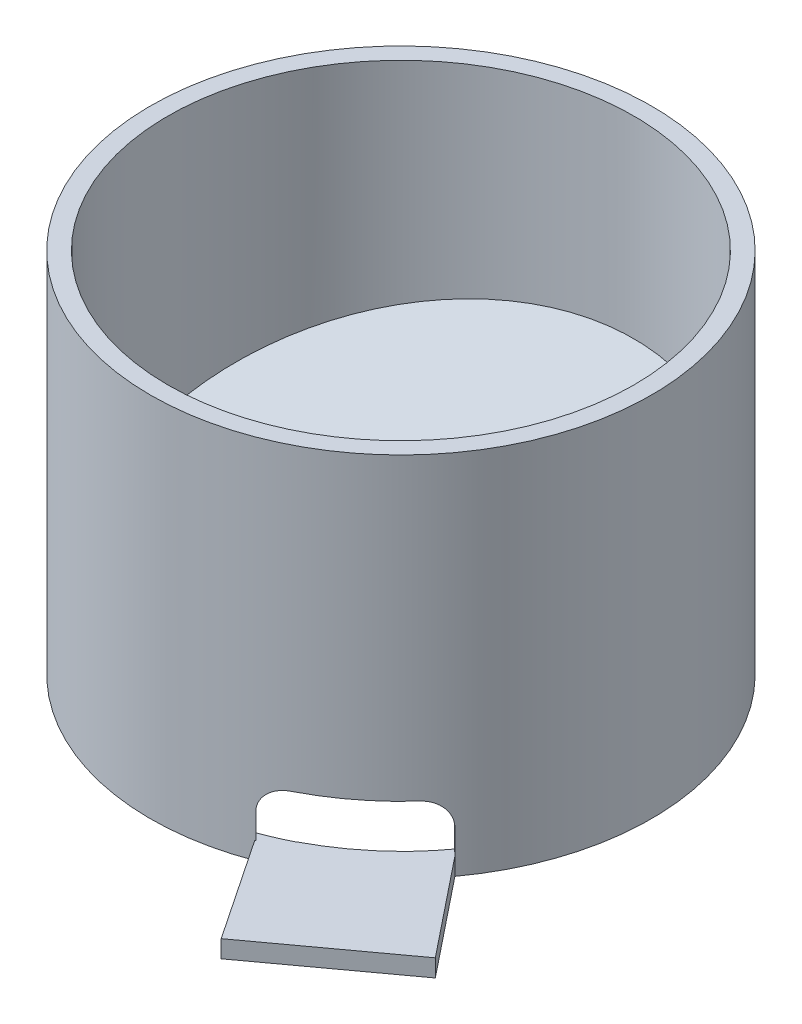
SolidWorks part; units mm, degrees
ref_plane "Front Plane" through (0, 0, 0) normal (0, 0, 1) x (1, 0, 0)
ref_plane "Top Plane" through (0, 0, 0) normal (0, 1, 0) x (1, 0, 0)
ref_plane "Right Plane" through (0, 0, 0) normal (1, 0, 0) x (0, 0, -1)
sketch "Sketch1" plane through (0, 0, 0) normal (0, 1, 0) x (1, 0, 0)
  line L0 (-85.6178, 0) -> (101.9259, 0) construction
  line L1 (0, 82.0843) -> (0, -78.0073) construction
  circle A0 centre (0, 0) radius 40
  circle A1 centre (0, 0) radius 43
extrude "Boss-Extrude1" add sketch "Sketch1" along normal blind 63
ref_plane "Plane1" through (0, 0, 0) normal (0, -1, 0) x (-1, 0, 0)
sketch "Sketch2" plane through (0, 0, 0) normal (0, -1, 0) x (-1, 0, 0)
  line L0 (-73.177, 0) -> (71.4567, 0) construction
  line L1 (0, 50.2844) -> (0, -53.4602) construction
  circle A0 centre (0, 0) radius 41.5
  circle A1 centre (0, 0) radius 40
extrude "Cut-Extrude1" cut sketch "Sketch2" against normal blind 3
sketch "Sketch4" plane through (0, 0, 0) normal (1, 0, 0) x (0, 0, -1)
  line L0 (-60.3433, 3) -> (63.2119, 3) construction
  line L1 (-47.3, 0) -> (47.3, 0) construction
  line L2 (-60.3433, 13) -> (63.2119, 13) construction
  line L3 (43, 86.4411) -> (43, -21.9512) construction
  line L4 (-43, 84.1892) -> (-43, -16.6967) construction
  line L5 (-23, 70.4828) -> (-23, -8.429) construction
  line L12 (-23, 13) -> (43, 30.6846)
  line L13 (-23, 13) -> (-15, 13)
  line L14 (-15, 13) -> (43, 28.5411)
  line L15 (43, 30.6846) -> (43, 28.5411)
  dimension "D1" = 3
  dimension "D2" = 10
  dimension "D3" = 43
  dimension "D4" = 86
  dimension "D5" = 20
  dimension "D6" = 15
  dimension "D7" = 8
extrude "Boss-Extrude2" add sketch "Sketch4" against normal up to next and the other way up to next
sketch "Sketch5" plane through (0, 63, 0) normal (0, 1, 0) x (1, 0, 0)
  line L0 (32.7261, -23) -> (105.2658, -23) construction
  line L1 (31.0311, -29.7669) -> (84.0329, 25.4858) construction
  line L2 (84.0329, 25.4858) -> (9.9287, -51.7655) construction
  line L3 (7.7491, -54.0377) -> (34.9544, -25.677)
  line L4 (34.9544, -25.677) -> (36.517, -27.176)
  line L5 (36.517, -27.176) -> (9.3117, -55.5366)
  line L6 (9.3117, -55.5366) -> (7.7491, -54.0377)
  circle A0 centre (0, 0) radius 43 construction
extrude "Boss-Extrude3" add sketch "Sketch5" against normal blind 70 separate body
sketch "Sketch6" plane through (32.5937, 0, 31.2659) normal (0.7217, 0, 0.6923) x (0.6923, 0, -0.7217)
  line L0 (-49.5886, 3) -> (66.7958, 3) construction
  line L1 (-47.3, 0) -> (47.3, 0) construction
  line L2 (-49.5886, 11.5) -> (49.8596, 11.5) construction
  line L3 (-14.1825, 19.6565) -> (-14.1825, -5.851) construction
  line L4 (1.4175, 17.7977) -> (1.4175, -9.3621) construction
  line L5 (5.6675, -7) -> (5.6675, 63) construction
  line L6 (-23.3582, 7.25) -> (33.3365, 7.25) construction
  line L7 (-18.4325, 7.25) -> (-18.4325, 3)
  line L9 (5.6675, 3) -> (-18.4325, 3)
  line L10 (-14.1825, 11.5) -> (1.4175, 11.5)
  line L11 (5.6675, 7.25) -> (5.6675, 3)
  arc A0 (5.6675, 7.25) -> (1.4175, 11.5) centre (1.4175, 7.25) ccw
  arc A1 (-14.1825, 11.5) -> (-18.4325, 7.25) centre (-14.1825, 7.25) ccw
  dimension "D1" = 3
  dimension "D2" = 8.5
  dimension "D3" = 4.25
  dimension "D4" = 15.6
  dimension "D5" = 4.25
extrude "Cut-Extrude2" cut sketch "Sketch6" against normal up to surface (5.5689 mm away)
sketch "Sketch7" plane through (0, 63, 0) normal (0, 1, 0) x (1, 0, 0)
  line L0 (34.9544, -25.677) -> (36.517, -27.176)
  line L1 (36.517, -27.176) -> (9.3117, -55.5366)
  line L2 (9.3117, -55.5366) -> (7.7491, -54.0377)
  line L3 (7.7491, -54.0377) -> (34.9544, -25.677)
extrude "Cut-Extrude3" cut sketch "Sketch7" against normal through all
sketch "Sketch9" plane through (0, 0, 0) normal (0, -1, 0) x (-1, 0, 0)
  line L0 (0, 0) -> (-21.008, -56.202) construction
  line L1 (0, 0) -> (-48.7033, -35.0427) construction
  line L2 (-21.008, -56.202) -> (-48.7033, -35.0427) construction
  dimension "D1" = 60
  dimension "D2" = 60
ref_plane "Plane3" through (0, 3, 0) normal (0, 1, 0) x (1, 0, 0)
sketch "Sketch11" plane through (0, 3, 0) normal (0, 1, 0) x (1, 0, 0)
  line L0 (14.9059, -39.8772) -> (26.8812, -57.7334) construction
  line L1 (0, 0) -> (21.008, -56.202) construction
  line L2 (34.6837, -25.4173) -> (48.1124, -42.2078) construction
  line L3 (14.9059, -39.8772) -> (34.6837, -25.4173)
  line L4 (34.6837, -25.4173) -> (48.1124, -42.2078)
  line L5 (48.1124, -42.2078) -> (26.8812, -57.7334)
  line L6 (26.8812, -57.7334) -> (14.9059, -39.8772)
  dimension "D1" = 24.5
  dimension "D2" = 21.5
  dimension "D3" = 21.5
extrude "Boss-Extrude6" add sketch "Sketch11" against normal blind 3
ref_plane "Plane4" through (0, 0, 0) normal (0, -1, 0) x (-1, 0, 0)
sketch "Sketch12" plane through (0, 0, 0) normal (0, -1, 0) x (-1, 0, 0)
  line L0 (-29.8293, -26.6499) -> (-31.9955, -28.7278) construction
  line L1 (0, 0) -> (-21.008, -56.202) construction
  line L2 (-30.9124, -27.6889) -> (-14.5306, -38.873)
  arc A0 (-30.9124, -27.6889) -> (-14.5306, -38.873) centre (0.8702, 1.2744) ccw
  arc A1 (-18.9486, -36.9215) -> (-29.4344, -29.2552) centre (0, 0) ccw construction
  dimension "D1" = 43
extrude "Cut-Extrude4" cut sketch "Sketch12" against normal blind 4
ref_plane "Plane5" through (0, 3, 0) normal (0, 1, 0) x (1, 0, 0)
ref_plane "Plane6" through (36.8745, 0, 50.4257) normal (0.5903, 0, 0.8072) x (0.8072, 0, -0.5903)
sketch "Sketch14" plane through (36.8745, 0, 50.4257) normal (0.5903, 0, 0.8072) x (0.8072, 0, -0.5903)
  line L0 (0, 18.1867) -> (0, -14.0358) construction
  line L1 (-32.3374, 0) -> (29.4808, 0) construction
  line L2 (-50.1118, 0) -> (50.1118, 0) construction
sketch "Sketch15" plane through (0, 3, 0) normal (0, 1, 0) x (1, 0, 0)
  line L0 (7.678, -66.085) -> (57.9245, -27.9902) construction
  line L1 (57.9245, -27.9902) -> (61.3594, -32.5208) construction
  line L2 (10.7716, -69.5137) -> (60.6714, -33.0239) construction
  point P2 (57.9245, -27.9902)
